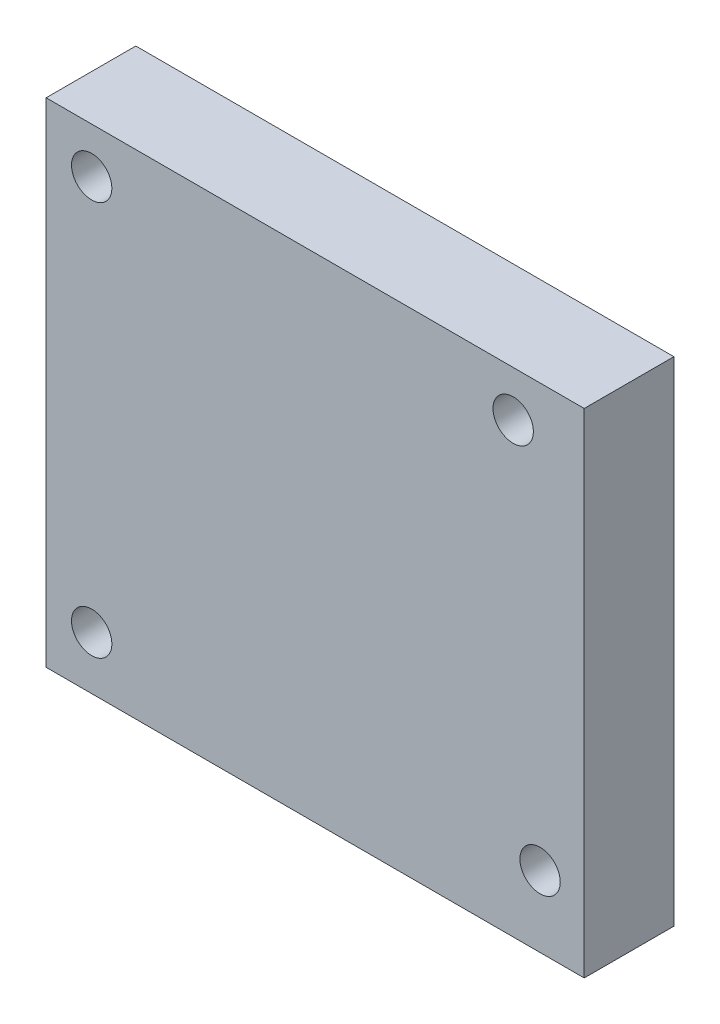
SolidWorks part; units mm, degrees
ref_plane "Front Plane" through (0, 0, 0) normal (0, 0, 1) x (1, 0, 0)
ref_plane "Top Plane" through (0, 0, 0) normal (0, 1, 0) x (1, 0, 0)
ref_plane "Right Plane" through (0, 0, 0) normal (1, 0, 0) x (0, 0, -1)
sketch "Sketch1" plane through (0, 0, 0) normal (0, 0, 1) x (1, 0, 0)
  line L0 (19.83, 19.92) -> (22.08, 19.92) construction
  line L1 (-30, -30) -> (30, -30)
  line L2 (-30, -30) -> (-30, 25)
  line L3 (-30, 25) -> (30, 25)
  line L4 (30, -30) -> (30, 25)
  line L7 (-24.92, -24.08) -> (-22.67, -24.08) construction
  line L8 (-24.92, -24.08) -> (-24.92, -21.83) construction
  line L9 (-24.92, 19.92) -> (-22.67, 19.92) construction
  line L11 (-24.92, -24.08) -> (-23.313, -22.5051) construction
  line L13 (-24.92, 17.67) -> (-24.92, 19.92) construction
  line L14 (25.08, -22.08) -> (25.08, -19.83) construction
  line L15 (20.7839, 18.0808) -> (22.08, 19.92) construction
  line L20 (0, 25) -> (0, 0) construction
  line L21 (25.08, -22.08) -> (22.83, -22.08) construction
  circle A0 centre (-24.92, 19.92) radius 2.25
  circle A1 centre (-24.92, -24.08) radius 2.25
  circle A2 centre (25.08, -22.08) radius 2.25
  circle A3 centre (22.08, 19.92) radius 2.25
  point P0 (0, 0)
  point P6 (-2.7982, -2.4)
  point P21 (-24.7724, 20.8088)
  point P23 (-22.1218, 22.32)
  dimension "D3" = 4.5
  dimension "D1" = 60
  dimension "D2" = 55
  dimension "D4" = 47
  dimension "D5" = 25
  dimension "D6" = 44
  dimension "D7" = 50
  dimension "D8" = 42
  dimension "D9" = 5.08
  dimension "D10" = 5.08
extrude "Boss-Extrude1" add sketch "Sketch1" along normal blind 10
